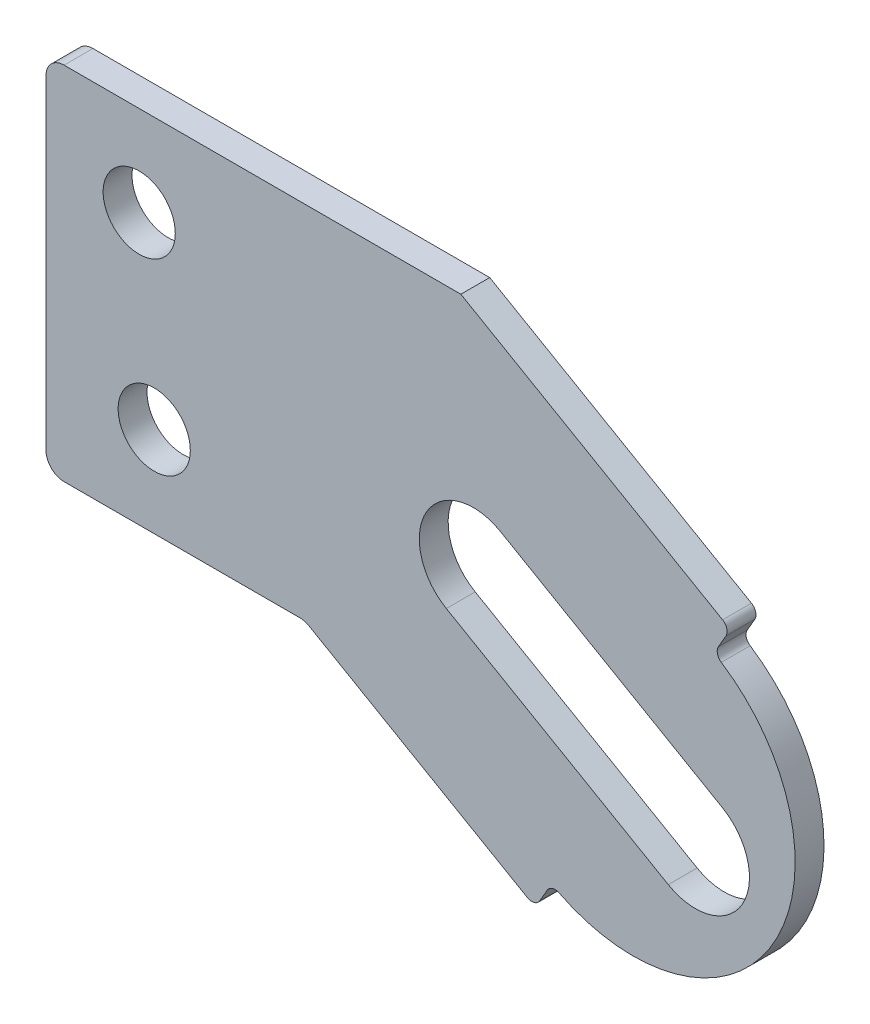
SolidWorks part; units mm, degrees
ref_plane "Front Plane" through (0, 0, 0) normal (0, 0, 1) x (1, 0, 0)
ref_plane "Top Plane" through (0, 0, 0) normal (0, 1, 0) x (1, 0, 0)
ref_plane "Right Plane" through (0, 0, 0) normal (1, 0, 0) x (0, 0, -1)
sketch "Sketch1" plane through (0, 0, 0) normal (0, 0, 1) x (1, 0, 0)
  line L0 (-4.5, 2.375) -> (-4.5, 0.125)
  line L1 (-4.375, 2.5) -> (-1.625, 2.5)
  line L2 (-1.625, 2.5) -> (-1.625, 0) construction
  line L3 (0, 0) -> (-1.5381, 0.888) construction
  line L4 (-1.625, 2.5) -> (0.1887, 1.4529)
  line L5 (-2.6779, -0.0167) -> (-1.1643, -0.8906)
  line L6 (-4.375, 0) -> (-2.7404, 0)
  line L7 (-0.1875, -0.3248) -> (-1.7256, 0.5633)
  line L8 (0.1875, 0.3248) -> (-1.3506, 1.2128)
  line L9 (0, 0) -> (1.3526, 2.3427) construction
  line L11 (0.2118, 1.3668) -> (0.1599, 1.277)
  line L12 (0.2118, 1.3668) -> (-1.0782, -0.8676) construction
  line L13 (-1.0782, -0.8676) -> (-1.0264, -0.7778)
  arc A0 (-2.7404, 0) -> (-2.6779, -0.0167) centre (-2.7404, -0.125) cw
  arc A1 (-4.5, 0.125) -> (-4.375, 0) centre (-4.375, 0.125) ccw
  arc A2 (-4.5, 2.375) -> (-4.375, 2.5) centre (-4.375, 2.375) cw
  circle A3 centre (-3.8541, 1.875) radius 0.25
  circle A4 centre (-3.75, 0.625) radius 0.25
  arc A5 (-0.1875, -0.3248) -> (0.1875, 0.3248) centre (0, 0) ccw
  arc A6 (-1.3506, 1.2128) -> (-1.7256, 0.5633) centre (-1.5381, 0.888) ccw
  arc A7 (0.1801, 1.1927) -> (-0.9433, -0.7531) centre (-0.4332, 0.2496) cw
  arc A8 (0.2118, 1.3668) -> (0.1887, 1.4529) centre (0.1572, 1.3983) ccw
  arc A9 (0.1599, 1.277) -> (0.1801, 1.1927) centre (0.2145, 1.2455) ccw
  arc A10 (-1.1643, -0.8906) -> (-1.0782, -0.8676) centre (-1.1328, -0.8361) ccw
  arc A11 (-0.9433, -0.7531) -> (-1.0264, -0.7778) centre (-0.9718, -0.8093) ccw
  point P6 (0, 0)
  point P11 (-2.7069, 0)
  point P14 (-4.5, 0)
  point P17 (-4.5, 2.5)
  point P23 (-0.769, 0.444)
  point P30 (0, 0)
  point P33 (-1.0845, -0.8765)
  point P42 (0, 0)
  point P46 (0, 0)
  dimension "D8" = 0.125
  dimension "D9" = 0.5
  dimension "D10" = 0.5
  dimension "D20" = 1.125
  dimension "D21" = 0.126
  dimension "D22" = 0.126
  dimension "D24" = 0.126
  dimension "D25" = 0.126
  dimension "D1" = 2.5
  dimension "D2" = 4.5
  dimension "D3" = 2.5
  dimension "D4" = 2.875
  dimension "D5" = 150
  dimension "D6" = 2.706
  dimension "D7" = 1.7931
  dimension "D11" = 1.875
  dimension "D12" = 0.625
  dimension "D13" = 0.75
  dimension "D14" = 0.6459
  dimension "D15" = 1.776
  dimension "D16" = 0.75
  dimension "D18" = 2.0952
  dimension "D19" = 0.1632
  dimension "D23" = 0.1528
extrude "Boss-Extrude5" add sketch "Sketch1" along normal blind 0.2
